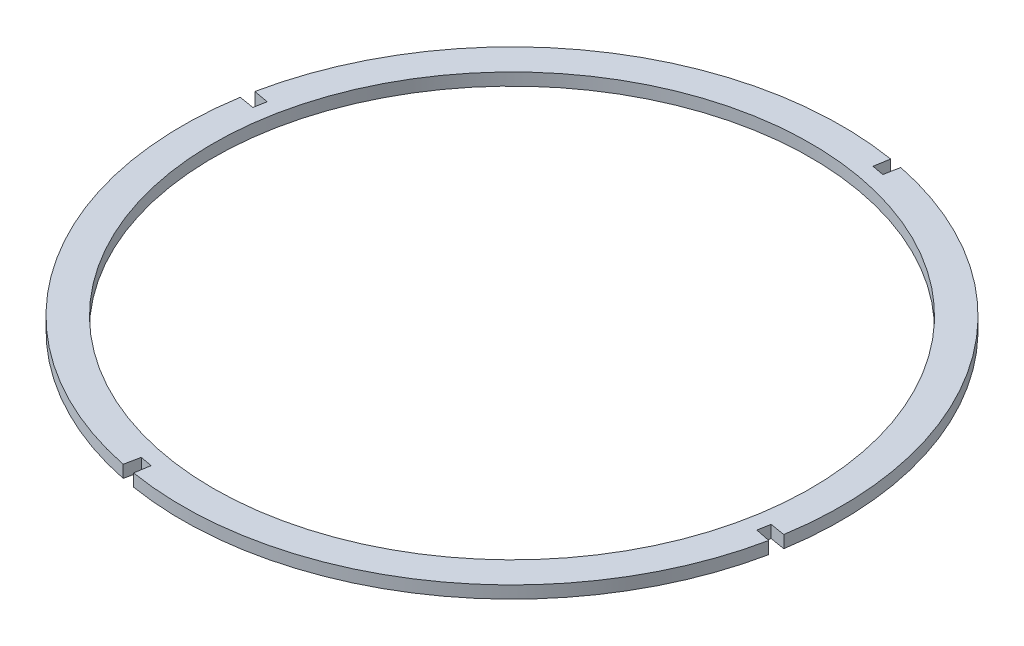
SolidWorks part; units mm, degrees
ref_plane "Спереди" through (0, 0, 0) normal (0, 0, 1) x (1, 0, 0)
ref_plane "Сверху" through (0, 0, 0) normal (0, 1, 0) x (1, 0, 0)
ref_plane "Справа" through (0, 0, 0) normal (1, 0, 0) x (0, 0, -1)
other "Configuration Table"
sketch "Эскиз1" plane through (0, 0, 0) normal (0, 1, 0) x (1, 0, 0)
  line L0 (-414.4165, 590.4782) -> (-398.682, 587.5755)
  line L1 (-480.6631, 187.2758) -> (-406.5492, 589.0269) construction
  line L3 (-414.4165, 590.4782) -> (-411.1867, 610.1363)
  line L4 (-398.682, 587.5755) -> (-395.0672, 607.1702)
  line L6 (-406.5492, 589.0269) -> (-554.5446, -214.518) construction
  line L7 (-480.6631, 187.2758) -> (-78.912, 113.162) construction
  line L8 (-480.6631, 187.2758) -> (-882.4141, 261.3896) construction
  line L9 (-77.4607, 121.0293) -> (-80.3633, 105.2947)
  line L10 (-80.3633, 105.2947) -> (-60.8467, 101.2978)
  line L11 (-77.4607, 121.0293) -> (-57.8026, 117.7994)
  line L12 (-562.4123, -213.069) -> (-546.6769, -215.9671)
  line L13 (-562.4123, -213.069) -> (-566.3984, -232.5901)
  line L14 (-546.6769, -215.9671) -> (-549.895, -235.6248)
  line L15 (-880.9628, 269.2569) -> (-883.8654, 253.5224)
  line L16 (-880.9628, 269.2569) -> (-900.5575, 272.8716)
  line L17 (-883.8654, 253.5224) -> (-903.5235, 256.7522)
  arc A0 (-411.1867, 610.1363) -> (-900.5575, 272.8716) centre (-480.6631, 187.2758) ccw
  circle A1 centre (-480.6631, 187.2758) radius 388.53
  arc A2 (-57.8026, 117.7994) -> (-395.0672, 607.1702) centre (-480.6631, 187.2758) ccw
  arc A3 (-549.895, -235.6248) -> (-60.8467, 101.2978) centre (-480.6631, 187.2758) ccw
  arc A4 (-903.5235, 256.7522) -> (-566.3984, -232.5901) centre (-480.6631, 187.2758) ccw
  point P7 (-406.5492, 589.0269)
  point P13 (-554.5446, -214.518)
  point P16 (-78.912, 113.162)
  point P24 (-882.4141, 261.3896)
  dimension "D1" = 857.06
  dimension "D2" = 777.06
  dimension "D3" = 0
  dimension "D4" = 0
  dimension "D5" = 16
  dimension "D6" = 16
  dimension "D7" = 0
  dimension "D8" = 408.53
  dimension "D9" = 16
  dimension "D10" = 0
  dimension "D11" = 16
  dimension "D12" = 0
  dimension "D13" = 408.53
  dimension "D14" = 408.53
  dimension "D15" = 408.53
  dimension "D16" = 0
extrude "Бобышка-Вытянуть2" add sketch "Эскиз1" along normal blind 16
